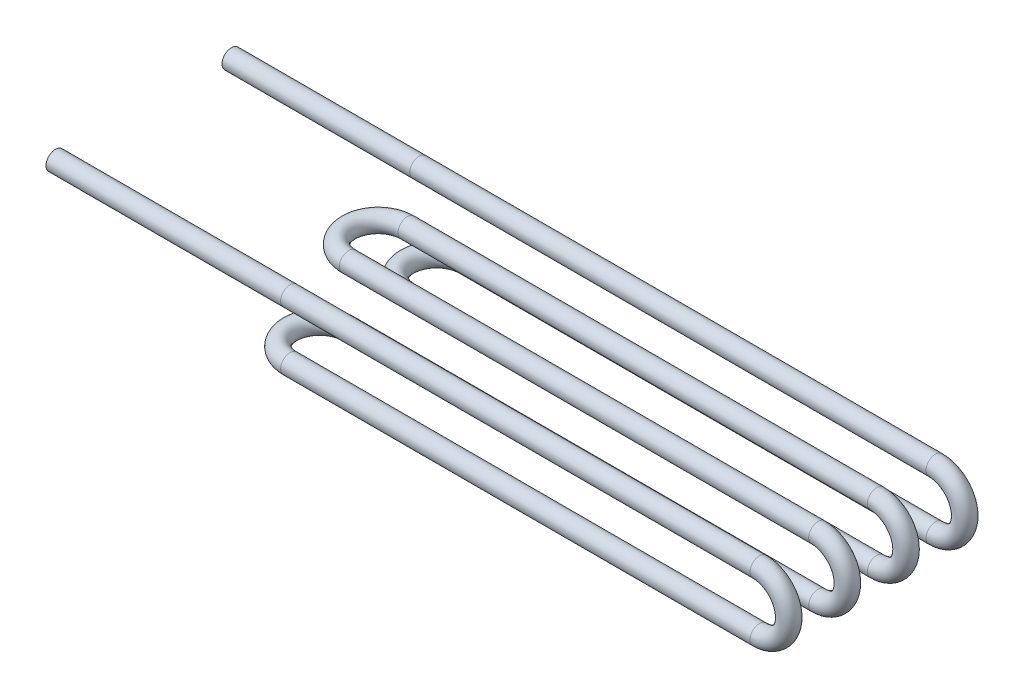
SolidWorks part; units mm, degrees
material "Copper"
ref_plane "Front Plane" through (0, 0, 0) normal (0, 0, 1) x (1, 0, 0)
ref_plane "Top Plane" through (0, 0, 0) normal (0, 1, 0) x (1, 0, 0)
ref_plane "Right Plane" through (0, 0, 0) normal (1, 0, 0) x (0, 0, -1)
sketch3d "3DSketch1"
  line L0 (0, 0, 0) -> (220, 0, 0)
  line L2 (220, -25, 0) -> (20, -25, 0)
  line L3 (20, -25, 74.9992) -> (220, -25, 74.9992)
  line L5 (20, -24.8345, 24.9995) -> (220, -24.8345, 24.9995)
  line L7 (220, 0.1655, 24.9995) -> (20, 0.1655, 24.9995)
  line L8 (220, 0, 74.9992) -> (20, 0, 74.9992)
  line L9 (20, 0.1655, 49.9995) -> (220, 0.1655, 49.9995)
  line L10 (20, 0, 74.9992) -> (-80, 0, 74.9992)
  line L11 (220, -24.8345, 49.9998) -> (20, -24.8345, 49.9998)
  line L12 (0, 0, 0) -> (-80, 0, 0)
  arc A0 (220, 0, 0) -> (220, -25, 0) centre (220, -12.5, 0) cw
  arc A1 (220, 0.1655, 24.9995) -> (220, -24.8345, 24.9995) centre (220, -12.3345, 24.9995) cw
  arc A2 (220, 0.1655, 49.9995) -> (220, -24.8345, 49.9998) centre (220, -12.3345, 49.9996) cw
  arc A3 (20, 0.1655, 49.9995) -> (20, 0.1655, 24.9995) centre (20, 0.1655, 37.4995) cw
  arc A4 (20, -25, 0) -> (20, -24.8345, 24.9995) centre (20, -24.9172, 12.4997) cw
  arc A5 (20, -24.8345, 49.9998) -> (20, -25, 74.9992) centre (20, -24.9172, 62.4995) cw
  arc A6 (220, 0, 74.9992) -> (220, -25, 74.9992) centre (220, -12.5, 74.9992) cw
  point P9 (20, -12.4175, 62.5823)
  point P15 (220, -12.5, -12.5)
  point P19 (220, -12.3345, 12.4995)
  point P23 (220, -12.3346, 37.4996)
  point P27 (20, -12.3345, 37.4995)
  point P31 (20, -12.4175, 12.417)
  point P35 (220, -12.5, 62.4992)
  dimension "D2" = 12.5
  dimension "D1" = 220
  dimension "D3" = 80
  dimension "D4" = 200
  dimension "D5" = 25
ref_plane "Plane1" through (-80, 0, 0) normal (1, 0, 0) x (0, 0, -1)
sketch "Sketch2" plane through (-80, 0, 0) normal (1, 0, 0) x (0, 0, -1)
  circle A0 centre (0, 0) radius 4
  circle A1 centre (0, 0) radius 3
  dimension "D1" = 8
  dimension "D2" = 6
sweep "Sweep1" add profiles "Sketch2" path "3DSketch1"
